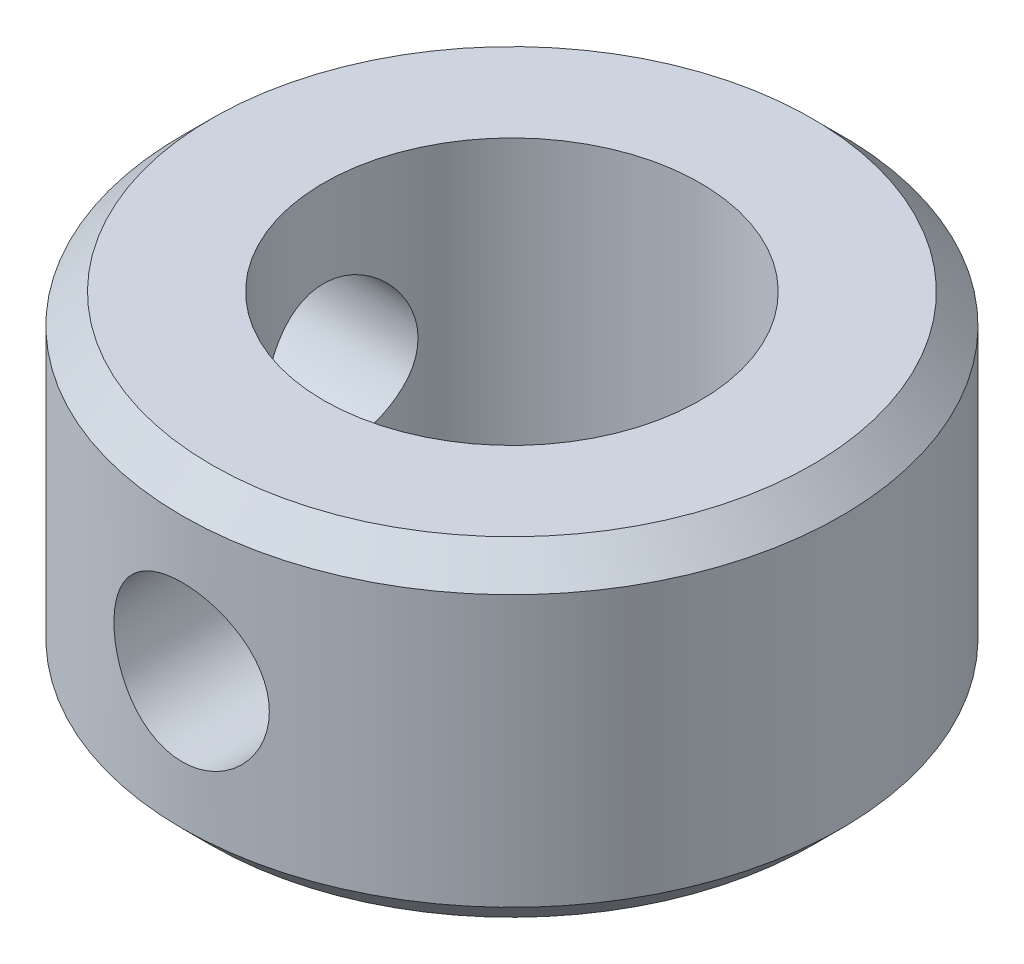
SolidWorks part; units mm, degrees
material "AISI 304"
ref_plane "Front Plane" through (0, 0, 0) normal (0, 0, 1) x (1, 0, 0)
ref_plane "Top Plane" through (0, 0, 0) normal (0, 1, 0) x (1, 0, 0)
ref_plane "Right Plane" through (0, 0, 0) normal (1, 0, 0) x (0, 0, -1)
sketch "Sketch1" plane through (0, 0, 0) normal (0, 1, 0) x (1, 0, 0)
  circle A0 centre (0, 0) radius 7
  circle A1 centre (0, 0) radius 4
  dimension "D1" = 8
  dimension "D2" = 14
extrude "Boss-Extrude1" add sketch "Sketch1" along normal mid plane 7
ref_plane "Plane1" through (0, 0, 7) normal (0, 0, 1) x (1, 0, 0)
hole_wizard "M4x0.7 Tapped Hole1" positions "Sketch2" profile "Sketch3" tap size "M4x0.7" standard "ANSI Metric"
sketch "Sketch2" plane through (0, 0, 7) normal (0, 0, 1) x (1, 0, 0)
  point P0 (0, 0)
sketch "Sketch3" plane through (0, 0, 7) normal (1, 0, 0) x (0, -1, 0)
  line L0 (0, 0) -> (0, 3)
  line L1 (0, 3) -> (1.65, 3)
  line L2 (1.65, 3) -> (1.65, 0)
  line L5 (1.65, 0) -> (0, 0)
  line L11 (0, -6.35) -> (0, 107.95) construction
  dimension "Thru Tap Drill Dia." = 3.3
  dimension "Thru Tap Drill Depth" = 3
cosmetic thread "Hole Thread1"
chamfer "Chamfer1" distance 0.625 angle 45 2 edges at (0, -3.5, 7) (0, 3.5, 7)
ref_axis "Axis1" through (0, 3.5, 0) along (0, -1, 0)
pattern_circular "CirPattern1" count 2 over 90 about axis through (0, 3.5, 0) along (0, -1, 0) of "M4x0.7 Tapped Hole1"
cosmetic thread "Hole Thread2"
